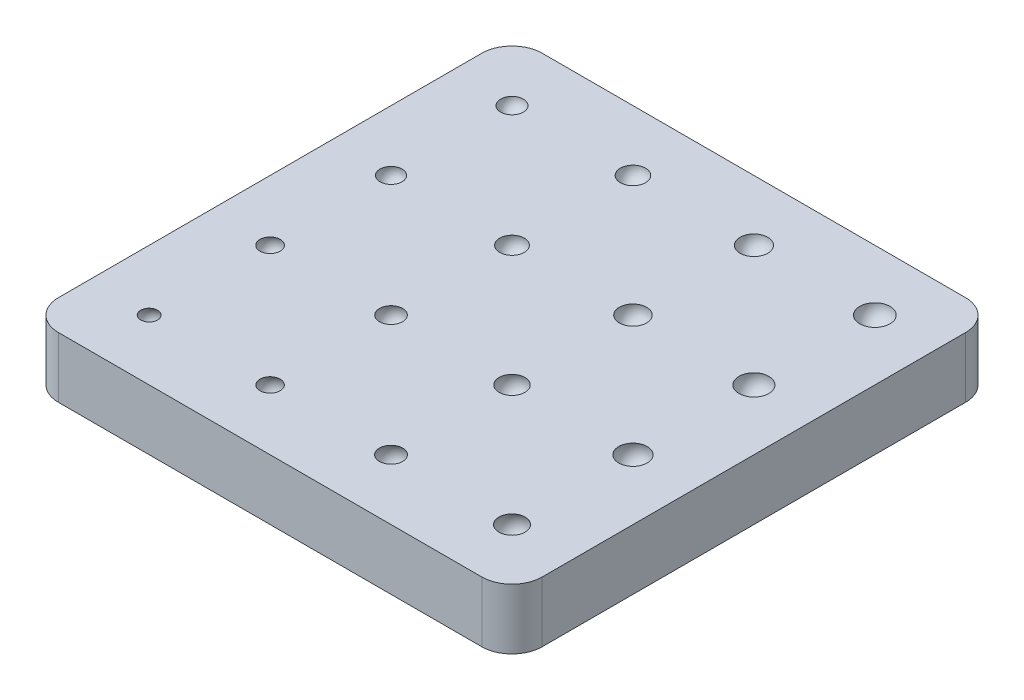
SolidWorks part; units mm, degrees
ref_plane "Front Plane" through (0, 0, 0) normal (0, 0, 1) x (1, 0, 0)
ref_plane "Top Plane" through (0, 0, 0) normal (0, 1, 0) x (1, 0, 0)
ref_plane "Right Plane" through (0, 0, 0) normal (1, 0, 0) x (0, 0, -1)
sketch "Sketch1" plane through (0, 0, 0) normal (0, 1, 0) x (1, 0, 0)
  line L1 (-50.8, -50.8) -> (50.8, -50.8)
  line L2 (-50.8, -50.8) -> (-50.8, 50.8)
  line L3 (-50.8, 50.8) -> (50.8, 50.8)
  line L4 (50.8, -50.8) -> (50.8, 50.8)
  line L5 (-50.8, -50.8) -> (50.8, 50.8) construction
  line L6 (-50.8, 50.8) -> (50.8, -50.8) construction
  point P0 (0, 0)
  dimension "D1" = 101.6
  dimension "D2" = 101.6
extrude "Boss-Extrude1" add sketch "Sketch1" along normal blind 12.7
sketch "Sketch2" plane through (0, 12.7, 0) normal (0, 1, 0) x (1, 0, 0)
  line L2 (-50.8, 50.8) -> (-38.1, 50.8) construction
  line L3 (-50.8, 50.8) -> (-50.8, 38.1) construction
  line L5 (-50.8, 38.1) -> (-38.1, 38.1) construction
  line L6 (-38.1, 50.8) -> (-38.1, 38.1) construction
  dimension "D1" = 12.7
ref_plane "Plane1" through (-38.1, 0, 0) normal (-1, 0, 0) x (0, 0, 1)
ref_plane "Plane2" through (-12.7, 0, 0) normal (-1, 0, 0) x (0, 0, 1)
ref_plane "Plane3" through (12.7, 0, 0) normal (-1, 0, 0) x (0, 0, 1)
ref_plane "Plane4" through (38.1, 0, 0) normal (-1, 0, 0) x (0, 0, 1)
ref_plane "Plane5" through (0, 0, 38.1) normal (0, 0, 1) x (1, 0, 0)
ref_plane "Plane6" through (0, 0, 12.7) normal (0, 0, 1) x (1, 0, 0)
ref_plane "Plane7" through (0, 0, -12.7) normal (0, 0, 1) x (1, 0, 0)
ref_plane "Plane8" through (0, 0, -38.1) normal (0, 0, 1) x (1, 0, 0)
ref_axis "Axis3" through (-38.1, 13.335, -38.1) along (0, -1, 0)
ref_axis "Axis4" through (-12.7, 13.335, -38.1) along (0, -1, 0)
ref_axis "Axis5" through (12.7, 13.335, -38.1) along (0, -1, 0)
ref_axis "Axis6" through (38.1, 13.335, -38.1) along (0, -1, 0)
ref_axis "Axis7" through (-38.1, -0.635, -12.7) along (0, 1, 0)
ref_axis "Axis8" through (-12.7, -0.635, -12.7) along (0, 1, 0)
ref_axis "Axis9" through (12.7, -0.635, -12.7) along (0, 1, 0)
ref_axis "Axis10" through (38.1, 13.335, -12.7) along (0, -1, 0)
ref_axis "Axis11" through (38.1, -0.635, 12.7) along (0, 1, 0)
ref_axis "Axis12" through (12.7, -0.635, 12.7) along (0, 1, 0)
ref_axis "Axis13" through (-12.7, 13.335, 12.7) along (0, -1, 0)
ref_axis "Axis14" through (-38.1, -0.635, 12.7) along (0, 1, 0)
ref_axis "Axis15" through (-38.1, -0.635, 38.1) along (0, 1, 0)
ref_axis "Axis16" through (-12.7, 13.335, 38.1) along (0, -1, 0)
ref_axis "Axis17" through (12.7, 13.335, 38.1) along (0, -1, 0)
ref_axis "Axis18" through (38.1, 13.335, 38.1) along (0, -1, 0)
sketch "Sketch3" plane through (-38.1, 0, 0) normal (-1, 0, 0) x (0, 0, 1)
  line L2 (-50.8, 12.7) -> (-38.1, 12.7) construction
  line L3 (-38.1, -6.985) -> (-38.1, 6.985) construction
  line L4 (-38.1, 15.0812) -> (-38.1, 10.3188)
  arc A0 (-38.1, 15.0812) -> (-38.1, 10.3188) centre (-38.1, 12.7) ccw
  dimension "D1" = 4.7625
revolve "Cut-Revolve2" cut sketch "Sketch3" angle 360 about axis through (-38.1, 13.335, -38.1) along (0, -1, 0)
sketch "Sketch4" plane through (-38.1, 0, 0) normal (-1, 0, 0) x (0, 0, 1)
  line L0 (38.1, -6.985) -> (38.1, 6.985) construction
  line L1 (-50.8, 12.7) -> (50.8, 12.7) construction
  line L2 (38.1, 13.4937) -> (38.1, 8.7312)
  arc A0 (38.1, 8.7312) -> (38.1, 13.4937) centre (38.1, 11.1125) ccw
  dimension "D1" = 4.7625
  dimension "D2" = 1.5875
revolve "Cut-Revolve3" cut sketch "Sketch4" angle 360 about axis through (-38.1, -0.635, 38.1) along (0, 1, 0)
sketch "Sketch5" plane through (-38.1, 0, 0) normal (-1, 0, 0) x (0, 0, 1)
  line L0 (12.7, -6.985) -> (12.7, 6.985) construction
  line L1 (-50.8, 12.7) -> (50.8, 12.7) construction
  line L2 (12.7, 14.0229) -> (12.7, 9.2604)
  arc A0 (12.7, 9.2604) -> (12.7, 14.0229) centre (12.7, 11.6417) ccw
  dimension "D1" = 4.7625
  dimension "D2" = 1.0583
revolve "Cut-Revolve4" cut sketch "Sketch5" angle 360 about axis through (-38.1, -0.635, 12.7) along (0, 1, 0)
sketch "Sketch6" plane through (-38.1, 0, 0) normal (-1, 0, 0) x (0, 0, 1)
  line L0 (-12.7, -6.985) -> (-12.7, 6.985) construction
  line L1 (-50.8, 12.7) -> (50.8, 12.7) construction
  line L2 (-12.7, 14.5521) -> (-12.7, 9.7896)
  arc A0 (-12.7, 9.7896) -> (-12.7, 14.5521) centre (-12.7, 12.1708) ccw
  dimension "D1" = 4.7625
  dimension "D2" = 0.5292
revolve "Cut-Revolve5" cut sketch "Sketch6" angle 360 about axis through (-38.1, -0.635, -12.7) along (0, 1, 0)
sketch "Sketch7" plane through (0, 0, -38.1) normal (0, 0, 1) x (1, 0, 0)
  line L0 (-12.7, 6.985) -> (-12.7, -6.985) construction
  line L1 (-12.7, 13.335) -> (-12.7, -0.635) construction
  line L2 (-12.7, 15.3458) -> (-12.7, 10.0542)
  line L4 (50.8, 12.7) -> (-50.8, 12.7) construction
  arc A0 (-12.7, 15.3458) -> (-12.7, 10.0542) centre (-12.7, 12.7) ccw
  dimension "D1" = 5.2917
revolve "Cut-Revolve6" cut sketch "Sketch7" angle 360 about axis through (-12.7, 13.335, -38.1) along (0, -1, 0)
sketch "Sketch8" plane through (0, 0, -38.1) normal (0, 0, 1) x (1, 0, 0)
  line L0 (12.7, 13.335) -> (12.7, -0.635) construction
  line L1 (50.8, 12.7) -> (-50.8, 12.7) construction
  line L2 (12.7, 15.6104) -> (12.7, 9.7896)
  arc A0 (12.7, 15.6104) -> (12.7, 9.7896) centre (12.7, 12.7) ccw
  dimension "D1" = 5.8208
revolve "Cut-Revolve7" cut sketch "Sketch8" angle 360 about axis through (12.7, 13.335, -38.1) along (0, -1, 0)
sketch "Sketch9" plane through (0, 0, -38.1) normal (0, 0, 1) x (1, 0, 0)
  line L0 (38.1, 6.985) -> (38.1, -6.985) construction
  line L1 (38.1, 13.335) -> (38.1, -0.635) construction
  line L2 (50.8, 12.7) -> (-50.8, 12.7) construction
  line L3 (38.1, 15.875) -> (38.1, 9.525)
  arc A0 (38.1, 15.875) -> (38.1, 9.525) centre (38.1, 12.7) ccw
  dimension "D1" = 6.35
revolve "Cut-Revolve8" cut sketch "Sketch9" angle 360 about axis through (38.1, 13.335, -38.1) along (0, -1, 0)
sketch "Sketch10" plane through (0, 0, -12.7) normal (0, 0, 1) x (1, 0, 0)
  line L0 (-12.7, 6.985) -> (-12.7, -6.985) construction
  line L1 (-12.7, 13.335) -> (-12.7, -0.635) construction
  line L2 (-50.8, 12.7) -> (50.8, 12.7) construction
  line L3 (-12.7, 14.8167) -> (-12.7, 9.525)
  arc A0 (-12.7, 9.525) -> (-12.7, 14.8167) centre (-12.7, 12.1708) ccw
  dimension "D1" = 5.2917
  dimension "D2" = 0.5292
revolve "Cut-Revolve9" cut sketch "Sketch10" angle 360 about axis through (-12.7, -0.635, -12.7) along (0, 1, 0)
sketch "Sketch11" plane through (0, 0, -12.7) normal (0, 0, 1) x (1, 0, 0)
  line L0 (12.7, 6.985) -> (12.7, -6.985) construction
  line L1 (12.7, 13.335) -> (12.7, -0.635) construction
  line L2 (-50.8, 12.7) -> (50.8, 12.7) construction
  line L3 (12.7, 15.0812) -> (12.7, 9.2604)
  arc A0 (12.7, 9.2604) -> (12.7, 15.0812) centre (12.7, 12.1708) ccw
  dimension "D1" = 5.8208
  dimension "D2" = 0.5292
revolve "Cut-Revolve10" cut sketch "Sketch11" angle 360 about axis through (12.7, -0.635, -12.7) along (0, 1, 0)
sketch "Sketch12" plane through (0, 0, -12.7) normal (0, 0, 1) x (1, 0, 0)
  line L0 (38.1, 6.985) -> (38.1, -6.985) construction
  line L1 (-50.8, 12.7) -> (50.8, 12.7) construction
  line L2 (38.1, 15.3458) -> (38.1, 8.9958)
  arc A0 (38.1, 8.9958) -> (38.1, 15.3458) centre (38.1, 12.1708) ccw
  dimension "D1" = 6.35
  dimension "D2" = 0.5292
revolve "Cut-Revolve11" cut sketch "Sketch12" angle 360 about axis through (38.1, 13.335, -12.7) along (0, -1, 0)
sketch "Sketch14" plane through (0, 0, 12.7) normal (0, 0, 1) x (1, 0, 0)
  line L0 (-12.7, 6.985) -> (-12.7, -6.985) construction
  line L1 (-12.7, 13.335) -> (-12.7, -0.635) construction
  line L2 (-50.8, 12.7) -> (50.8, 12.7) construction
  line L3 (-12.7, 14.2875) -> (-12.7, 8.9958)
  arc A0 (-12.7, 8.9958) -> (-12.7, 14.2875) centre (-12.7, 11.6417) ccw
  dimension "D1" = 5.2917
  dimension "D2" = 1.0583
revolve "Cut-Revolve12" cut sketch "Sketch14" angle 360 about axis through (-12.7, 13.335, 12.7) along (0, -1, 0)
sketch "Sketch15" plane through (0, 0, 12.7) normal (0, 0, 1) x (1, 0, 0)
  line L0 (12.7, 6.985) -> (12.7, -6.985) construction
  line L1 (12.7, 13.335) -> (12.7, -0.635) construction
  line L2 (-50.8, 12.7) -> (50.8, 12.7) construction
  line L3 (12.7, 14.5521) -> (12.7, 8.7312)
  arc A0 (12.7, 8.7312) -> (12.7, 14.5521) centre (12.7, 11.6417) ccw
  dimension "D1" = 5.8208
  dimension "D2" = 1.0583
revolve "Cut-Revolve13" cut sketch "Sketch15" angle 360 about axis through (12.7, -0.635, 12.7) along (0, 1, 0)
sketch "Sketch16" plane through (0, 0, 12.7) normal (0, 0, 1) x (1, 0, 0)
  line L0 (38.1, 6.985) -> (38.1, -6.985) construction
  line L1 (38.1, 13.335) -> (38.1, -0.635) construction
  line L2 (-50.8, 12.7) -> (50.8, 12.7) construction
  line L3 (38.1, 14.8167) -> (38.1, 8.4667)
  arc A0 (38.1, 8.4667) -> (38.1, 14.8167) centre (38.1, 11.6417) ccw
  dimension "D1" = 6.35
  dimension "D2" = 1.0583
revolve "Cut-Revolve14" cut sketch "Sketch16" angle 360 about axis through (38.1, -0.635, 12.7) along (0, 1, 0)
sketch "Sketch17" plane through (0, 0, 38.1) normal (0, 0, 1) x (1, 0, 0)
  line L0 (-12.7, 6.985) -> (-12.7, -6.985) construction
  line L1 (-12.7, 13.335) -> (-12.7, -0.635) construction
  line L2 (-50.8, 12.7) -> (50.8, 12.7) construction
  line L3 (-12.7, 13.7583) -> (-12.7, 8.4667)
  arc A0 (-12.7, 8.4667) -> (-12.7, 13.7583) centre (-12.7, 11.1125) ccw
  dimension "D1" = 5.2917
  dimension "D2" = 1.5875
revolve "Cut-Revolve15" cut sketch "Sketch17" angle 360 about axis through (-12.7, 13.335, 38.1) along (0, -1, 0)
sketch "Sketch18" plane through (0, 0, 38.1) normal (0, 0, 1) x (1, 0, 0)
  line L0 (12.7, 6.985) -> (12.7, -6.985) construction
  line L1 (12.7, 13.335) -> (12.7, -0.635) construction
  line L2 (12.7, 14.0229) -> (12.7, 8.2021)
  line L3 (-50.8, 12.7) -> (50.8, 12.7) construction
  arc A0 (12.7, 8.2021) -> (12.7, 14.0229) centre (12.7, 11.1125) ccw
  dimension "D1" = 5.8208
  dimension "D2" = 1.5875
revolve "Cut-Revolve16" cut sketch "Sketch18" angle 360 about axis through (12.7, 13.335, 38.1) along (0, -1, 0)
sketch "Sketch19" plane through (0, 0, 38.1) normal (0, 0, 1) x (1, 0, 0)
  line L0 (38.1, 6.985) -> (38.1, -6.985) construction
  line L1 (-50.8, 12.7) -> (50.8, 12.7) construction
  line L2 (38.1, 14.2875) -> (38.1, 7.9375)
  arc A0 (38.1, 7.9375) -> (38.1, 14.2875) centre (38.1, 11.1125) ccw
  dimension "D1" = 6.35
  dimension "D2" = 1.5875
revolve "Cut-Revolve17" cut sketch "Sketch19" angle 360 about axis through (38.1, 13.335, 38.1) along (0, -1, 0)
fillet "Fillet1" radius 6.35 4 edges at (-50.8, 6.35, -50.8) (50.8, 6.35, -50.8) (50.8, 6.35, 50.8) (-50.8, 6.35, 50.8)
